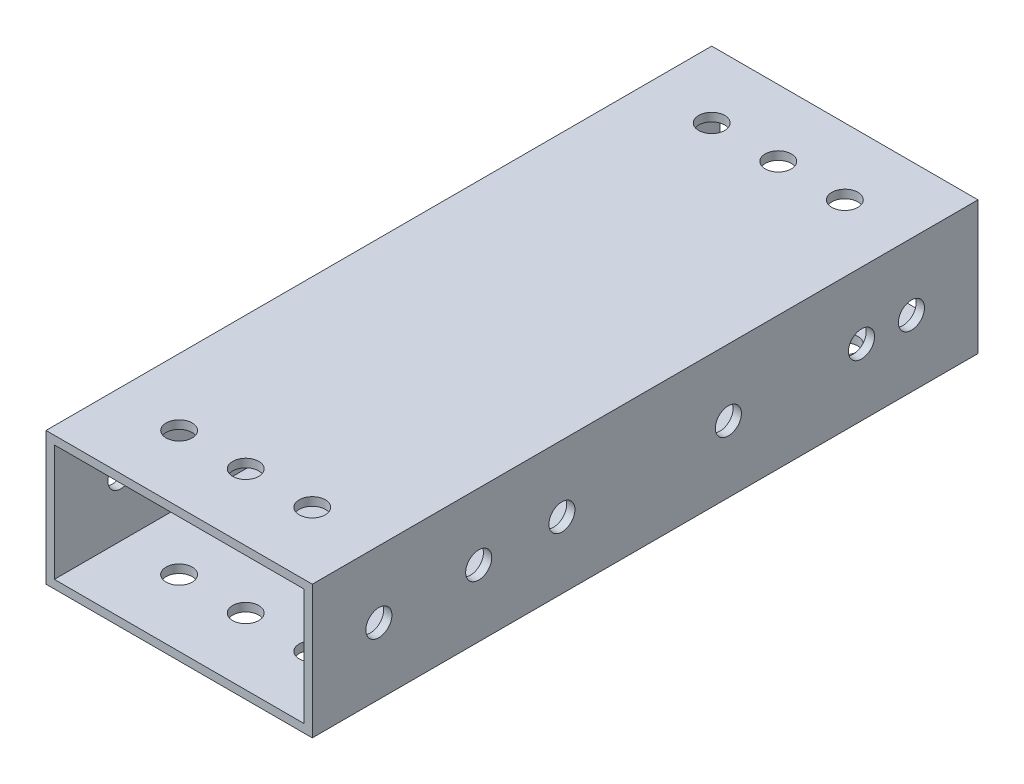
SolidWorks part; units mm, degrees
material "6061-T6 (SS)"
ref_plane "Front Plane" through (0, 0, 0) normal (0, 0, 1) x (1, 0, 0)
ref_plane "Top Plane" through (0, 0, 0) normal (0, 1, 0) x (1, 0, 0)
ref_plane "Right Plane" through (0, 0, 0) normal (1, 0, 0) x (0, 0, -1)
sketch "Sketch1" plane through (0, 0, 0) normal (0, 0, 1) x (1, 0, 0)
  line L0 (-23.8125, 11.1125) -> (23.8125, 11.1125)
  line L1 (-25.4, -12.7) -> (25.4, -12.7)
  line L2 (-25.4, -12.7) -> (-25.4, 12.7)
  line L3 (-25.4, 12.7) -> (25.4, 12.7)
  line L4 (25.4, -12.7) -> (25.4, 12.7)
  line L5 (-25.4, -12.7) -> (25.4, 12.7) construction
  line L6 (-25.4, 12.7) -> (25.4, -12.7) construction
  line L7 (23.8125, -11.1125) -> (23.8125, 11.1125)
  line L8 (-23.8125, -11.1125) -> (23.8125, -11.1125)
  line L9 (-23.8125, -11.1125) -> (-23.8125, 11.1125)
  point P0 (0, 0)
  dimension "D1" = 50.8
  dimension "D2" = 25.4
  dimension "D3" = 1.5875
extrude "Boss-Extrude1" add sketch "Sketch1" along normal mid plane 127
sketch "Sketch2" plane through (0, 12.7, 0) normal (0, 1, 0) x (1, 0, 0)
  line L0 (25.4, 63.5) -> (-25.4, 63.5) construction
  line L1 (25.4, 0) -> (-25.4, 0) construction
  line L2 (25.4, -63.5) -> (25.4, 63.5) construction
  line L3 (-25.4, -63.5) -> (-25.4, 63.5) construction
  circle A0 centre (-12.7, 50.8) radius 2.4892
  circle A1 centre (0, 50.8) radius 2.4892
  circle A2 centre (12.7, 50.8) radius 2.4892
  circle A3 centre (12.7, -50.8) radius 2.4892
  circle A4 centre (0, -50.8) radius 2.4892
  circle A5 centre (-12.7, -50.8) radius 2.4892
  dimension "D1" = 4.9784
  dimension "D2" = 12.7
  dimension "D3" = 12.7
  dimension "D4" = 12.7
extrude "Cut-Extrude1" cut sketch "Sketch2" against normal through all
sketch "Sketch3" plane through (25.4, 0, 0) normal (1, 0, 0) x (0, 0, -1)
  line L0 (0, 12.7) -> (0, -12.7) construction
  line L1 (-63.5, 12.7) -> (63.5, 12.7) construction
  line L2 (-63.5, -12.7) -> (63.5, -12.7) construction
  line L3 (-63.5, -12.7) -> (-63.5, 12.7) construction
  line L5 (63.5, -12.7) -> (63.5, 12.7) construction
  circle A8 centre (50.8, 0) radius 2.4892
  circle A9 centre (41.275, 0) radius 2.4892
  circle A10 centre (15.875, 0) radius 2.4892
  circle A11 centre (-50.8, 0) radius 2.4892
  circle A14 centre (-31.75, 0) radius 2.4892
  circle A15 centre (-15.875, 0) radius 2.4892
  dimension "D1" = 12.7
  dimension "D3" = 15.875
  dimension "D8" = 4.9784
  dimension "D2" = 31.75
  dimension "D4" = 22.225
  dimension "D7" = 25.4
extrude "Cut-Extrude2" cut sketch "Sketch3" against normal through all
